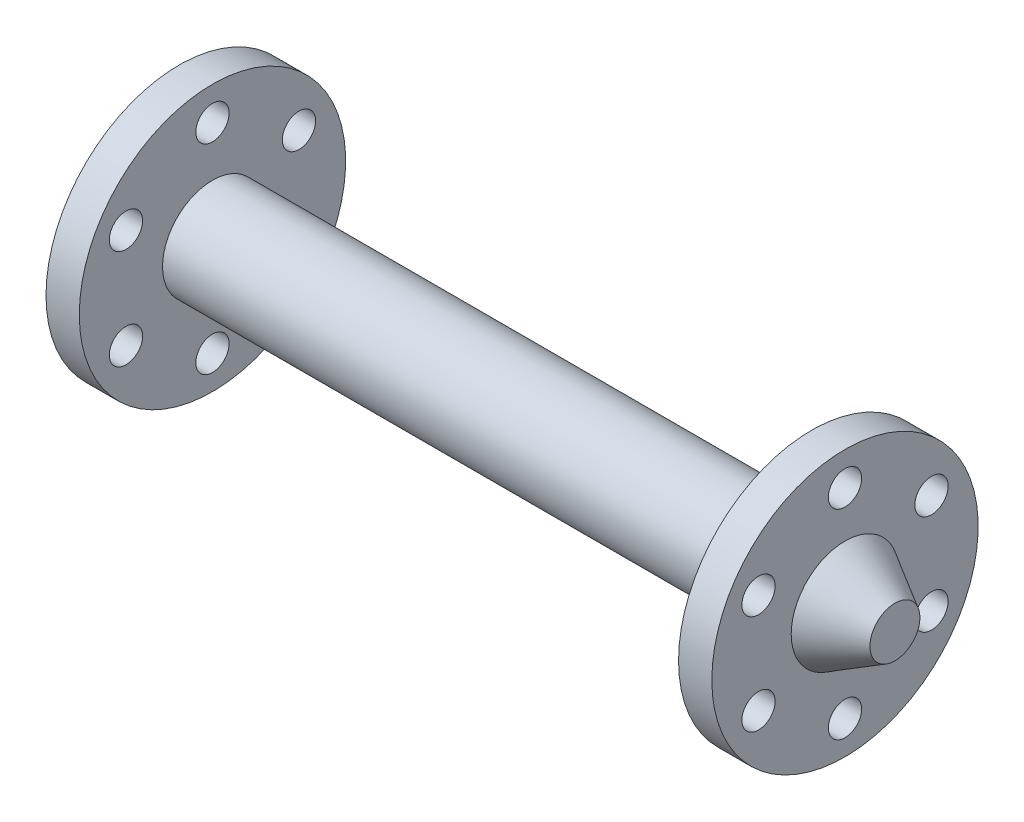
SolidWorks part; units mm, degrees
ref_plane "Front Plane" through (0, 0, 0) normal (0, 0, 1) x (1, 0, 0)
ref_plane "Top Plane" through (0, 0, 0) normal (0, 1, 0) x (1, 0, 0)
ref_plane "Right Plane" through (0, 0, 0) normal (1, 0, 0) x (0, 0, -1)
sketch "Sketch3" plane through (0, 0, 0) normal (0, 1, 0) x (1, 0, 0)
  line L0 (0, 0) -> (370, 0) construction
  line L1 (-40, 15) -> (-40, -15)
  line L2 (-10, 80) -> (10, 80)
  line L3 (-10, 80) -> (-10, -80)
  line L4 (-10, -80) -> (10, -80)
  line L5 (10, 80) -> (10, -80)
  line L6 (-10, 80) -> (10, -80) construction
  line L7 (-10, -80) -> (10, 80) construction
  line L8 (10, 30) -> (370, 30)
  line L9 (10, 30) -> (10, -30)
  line L10 (10, -30) -> (370, -30)
  line L11 (370, 30) -> (370, -30)
  line L12 (-40, 15) -> (-10, 32.3205)
  line L13 (-40, -15) -> (-10, -32.3205)
  line L14 (370, 0) -> (10, 0) construction
  line L15 (10, 0) -> (190, 0) construction
  line L16 (190, 0) -> (190, 30) construction
  line L17 (420, -15) -> (390, -32.3205)
  line L18 (420, 15) -> (420, -15)
  line L19 (420, 15) -> (390, 32.3205)
  line L20 (390, -80) -> (370, -80)
  line L21 (370, 80) -> (370, -80)
  line L22 (390, 80) -> (370, 80)
  line L23 (390, 80) -> (390, -80)
  line L24 (-40, 0) -> (420, 0)
  point P14 (-40, 0)
  dimension "D1" = 60
  dimension "D2" = 160
  dimension "D3" = 20
  dimension "D4" = 360
  dimension "D5" = 30
  dimension "D6" = 30
  dimension "D7" = 30
revolve "Revolve3" add sketch "Sketch3" angle 360 about L24
sketch "Sketch4" plane through (-10, 0, 0) normal (-1, 0, 0) x (0, 0, 1)
  circle A0 centre (0, 0) radius 60 construction
  circle A1 centre (0, 60) radius 10
  circle A2 centre (51.9615, 30) radius 10
  circle A3 centre (51.9615, -30) radius 10
  circle A4 centre (0, -60) radius 10
  circle A5 centre (-51.9615, -30) radius 10
  circle A6 centre (-51.9615, 30) radius 10
  point P17 (0, 0)
  dimension "D1" = 120
  dimension "D2" = 20
  dimension "D3" = 6
extrude "Cut-Extrude1" cut sketch "Sketch4" against normal through all both and the other way through all
